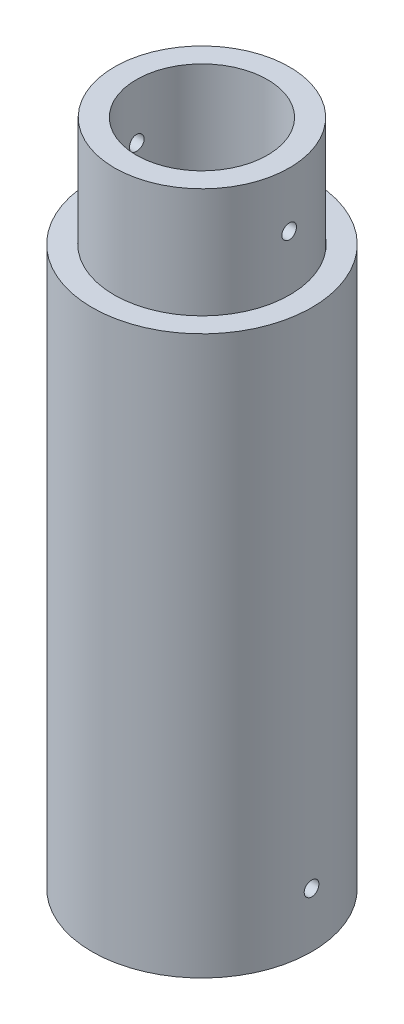
SolidWorks part; units mm, degrees
ref_plane "Front Plane" through (0, 0, 0) normal (0, 0, 1) x (1, 0, 0)
ref_plane "Top Plane" through (0, 0, 0) normal (0, 1, 0) x (1, 0, 0)
ref_plane "Right Plane" through (0, 0, 0) normal (1, 0, 0) x (0, 0, -1)
sketch "Sketch1" plane through (0, 0, 0) normal (0, 1, 0) x (1, 0, 0)
  circle A0 centre (0, 0) radius 15
  circle A1 centre (0, 0) radius 12
  dimension "D1" = 30
  dimension "D2" = 24
extrude "Boss-Extrude1" add sketch "Sketch1" along normal blind 76.2
sketch "Sketch2" plane through (0, 76.2, 0) normal (0, 1, 0) x (1, 0, 0)
  circle A0 centre (0, 0) radius 8.95
  circle A1 centre (0, 0) radius 11.95
  dimension "D1" = 17.9
  dimension "D2" = 23.9
extrude "Boss-Extrude2" add sketch "Sketch2" along normal blind 15 and the other way blind 3 separate body
sketch "Sketch3" plane through (0, 0, 0) normal (1, 0, 0) x (0, 0, -1)
  line L0 (0, 91.2) -> (0, 83.7) construction
  line L1 (11.95, 91.2) -> (-11.95, 91.2) construction
  line L2 (0, 7.5) -> (0, 0) construction
  circle A0 centre (0, 83.7) radius 1
  circle A1 centre (0, 7.5) radius 1
  dimension "D1" = 2
  dimension "D2" = 7.5
extrude "Cut-Extrude1" cut sketch "Sketch3" against normal through all and the other way through all
